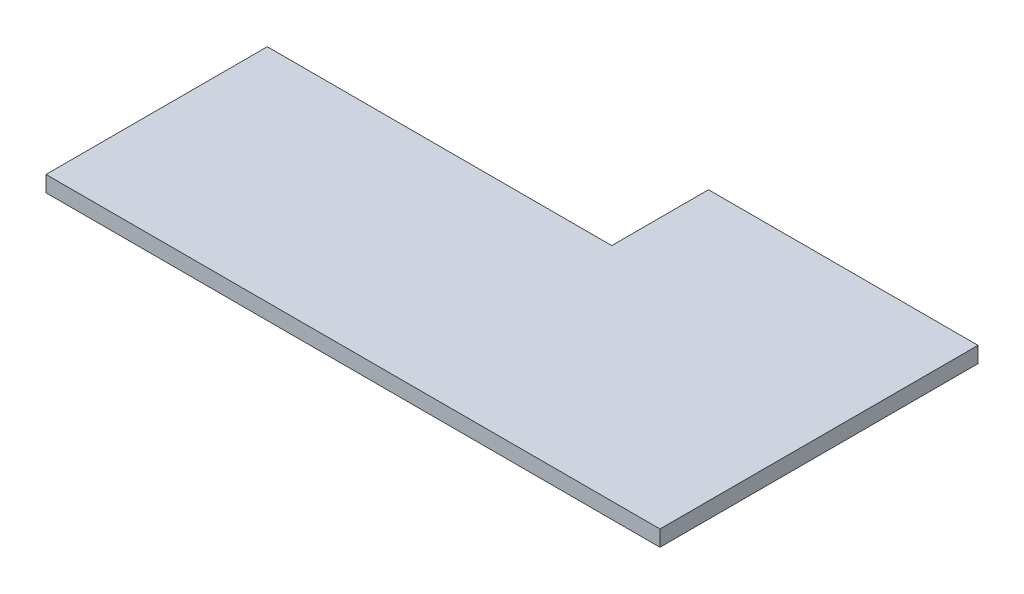
SolidWorks part; units mm, degrees
ref_plane "Front Plane" through (0, 0, 0) normal (0, 0, 1) x (1, 0, 0)
ref_plane "Top Plane" through (0, 0, 0) normal (0, 1, 0) x (1, 0, 0)
ref_plane "Right Plane" through (0, 0, 0) normal (1, 0, 0) x (0, 0, -1)
sketch "Sketch1" plane through (0, 0, 0) normal (0, 1, 0) x (1, 0, 0)
  line L0 (-63.91, 13.6221) -> (-63.91, -27.4279)
  line L13 (-63.91, -27.4279) -> (50, -27.4279)
  line L14 (50, -27.4279) -> (50, 16.5721)
  line L15 (50, 16.5721) -> (50, 31.5721)
  line L16 (50, 31.5721) -> (0, 31.5721)
  line L17 (0, 31.5721) -> (0, 13.6221)
  line L18 (0, 13.6221) -> (-63.91, 13.6221)
  point P0 (0, 0)
extrude "Boss-Extrude2" add sketch "Sketch1" along normal blind 2.95
